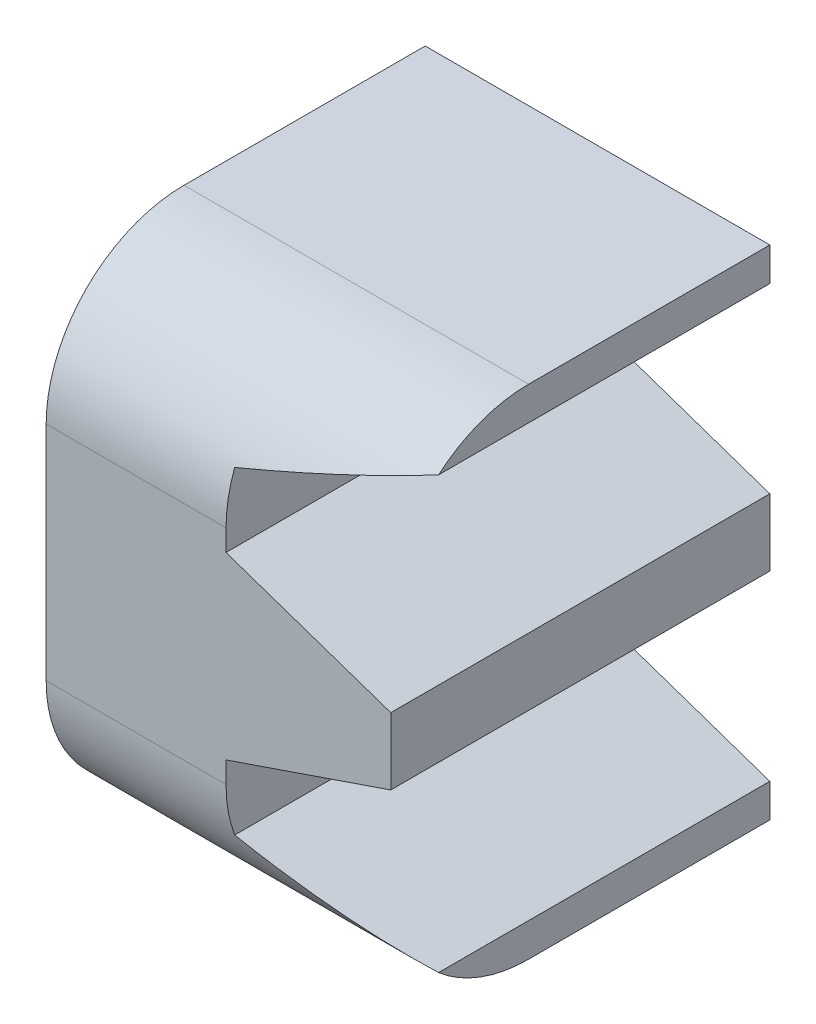
SolidWorks part; units mm, degrees
ref_plane "Front Plane" through (0, 0, 0) normal (0, 0, 1) x (1, 0, 0)
ref_plane "Top Plane" through (0, 0, 0) normal (0, 1, 0) x (1, 0, 0)
ref_plane "Right Plane" through (0, 0, 0) normal (1, 0, 0) x (0, 0, -1)
sketch "Sketch1" plane through (0, 0, 0) normal (0, 0, 1) x (1, 0, 0)
  line L81 (2.755, -3.6129) -> (2.755, -3.127)
  line L82 (2.755, -3.127) -> (0.3646, -2.3095)
  line L83 (0.3646, -2.3095) -> (0.3646, -1.3034)
  line L84 (0.3646, -1.3034) -> (2.755, -0.4859)
  line L85 (2.755, -0.4859) -> (2.755, 0.4859)
  line L86 (2.755, 0.4859) -> (0.3646, 1.3034)
  line L87 (0.3646, 1.3034) -> (0.3646, 2.3095)
  line L88 (0.3646, 2.3095) -> (2.755, 3.127)
  line L89 (2.755, 3.127) -> (2.755, 3.6129)
  line L168 (-2.245, -3.6129) -> (-2.245, 3.6129)
  line L169 (2.755, 3.6129) -> (-2.245, 3.6129)
  line L170 (2.755, -3.6129) -> (-2.245, -3.6129)
  dimension "D1" = 2.5263
extrude "Boss-Extrude1" add sketch "Sketch1" along normal blind 5.5 contours L168 L169 L89 L88 L87 L86 L85 L84 L83 L82 L81 L170
fillet "Fillet1" radius 2 2 edges at (0.255, -3.6129, 5.5) (0.255, 3.6129, 5.5)
